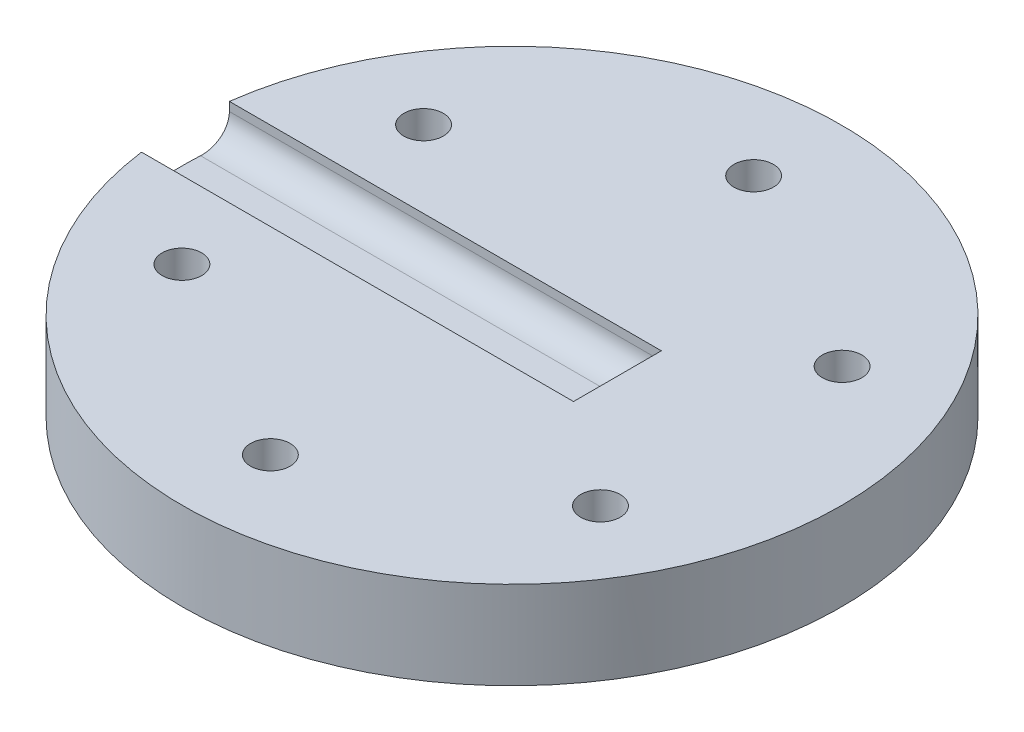
SolidWorks part; units mm, degrees
ref_plane "Front" through (0, 0, 0) normal (0, 0, 1) x (1, 0, 0)
ref_plane "Top" through (0, 0, 0) normal (0, 1, 0) x (1, 0, 0)
ref_plane "Right" through (0, 0, 0) normal (1, 0, 0) x (0, 0, -1)
sketch "Sketch1" plane through (0, 0, 0) normal (0, 1, 0) x (1, 0, 0)
  circle A0 centre (0, 0) radius 37.5
  circle A1 centre (0, 27.5) radius 2.25
  circle A2 centre (23.8157, 13.75) radius 2.25
  circle A3 centre (23.8157, -13.75) radius 2.25
  circle A4 centre (0, -27.5) radius 2.25
  circle A5 centre (-23.8157, -13.75) radius 2.25
  circle A6 centre (-23.8157, 13.75) radius 2.25
  point P18 (0, 0)
  dimension "D1" = 75
  dimension "D2" = 4.5
  dimension "D3" = 27.5
  dimension "D5" = 13.75
  dimension "D4" = 6
  dimension "D6" = 23.8157
  dimension "D7" = 60
extrude "Boss-Extrude1" add sketch "Sketch1" along normal blind 10
sketch "Sketch2" plane through (0, 10, 0) normal (0, 1, 0) x (1, 0, 0)
  line L0 (12, 0) -> (12, -5.6407)
  line L1 (0, 0) -> (12, 0) construction
  line L2 (12, 5) -> (-37.1652, 5)
  line L3 (12, -5) -> (-37.1652, -5)
  line L4 (12, 0) -> (12, 5)
  circle A1 centre (0, 0) radius 37.5 construction
  circle A2 centre (0, 0) radius 37.5
  dimension "D1" = 90
  dimension "D2" = 5
  dimension "D3" = 5
  dimension "D4" = 12
  dimension "D5" = 10
extrude "Cut-Extrude1" cut sketch "Sketch2" against normal blind 4
fillet "Fillet1" radius 3 3 edges at (-12.5826, 6, -5) (12, 6, 0) (-12.5826, 6, 5)
